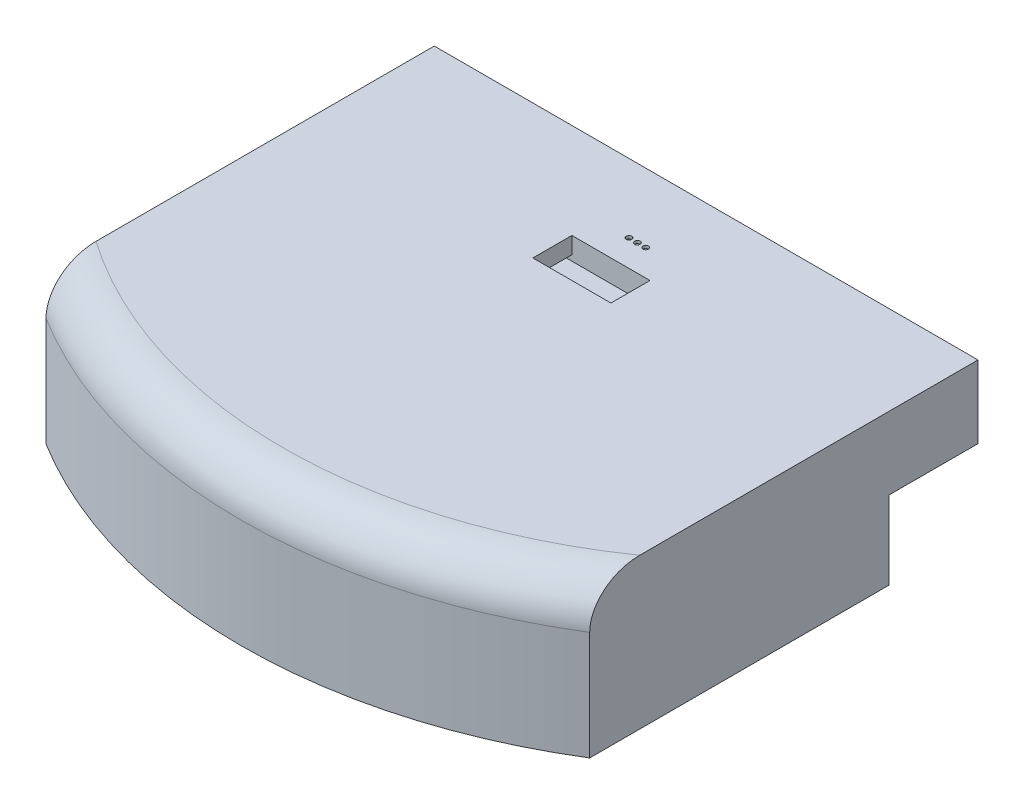
SolidWorks part; units mm, degrees
ref_plane "Front Plane" through (0, 0, 0) normal (0, 0, 1) x (1, 0, 0)
ref_plane "Top Plane" through (0, 0, 0) normal (0, 1, 0) x (1, 0, 0)
ref_plane "Right Plane" through (0, 0, 0) normal (1, 0, 0) x (0, 0, -1)
sketch "Sketch1" plane through (0, 0, 0) normal (0, 1, 0) x (1, 0, 0)
  line L0 (-97.5, -18.7714) -> (97.5, -18.7714)
  line L1 (97.5, -158.0314) -> (97.5, -18.7714)
  line L2 (-97.5, -18.7714) -> (-97.5, -158.0314)
  arc A0 (97.5, -158.0314) -> (-97.5, -158.0314) centre (0, 0) cw
  point P2 (0, 0)
  dimension "D2" = 195
  dimension "D3" = 139.26
extrude "Boss-Extrude1" add sketch "Sketch1" along normal blind 54
fillet "Fillet1" radius 15 1 edges at (0, 54, 185.6884)
sketch "Sketch2" plane through (-97.5, 0, 0) normal (-1, 0, 0) x (0, 0, 1)
  line L1 (18.7714, 0) -> (50.7714, 0)
  line L2 (18.7714, 0) -> (18.7714, 28)
  line L3 (18.7714, 28) -> (50.7714, 28)
  line L4 (50.7714, 0) -> (50.7714, 28)
  dimension "D1" = 28
  dimension "D2" = 32
extrude "Cut-Extrude1" cut sketch "Sketch2" against normal blind 445
sketch "Sketch3" plane through (0, 0, 0) normal (0, -1, 0) x (1, 0, 0)
  line L0 (0, 185.6884) -> (0, 159.7484)
  line L2 (-6.9, 159.7484) -> (6.9, 159.7484)
  line L3 (-6.9, 159.7484) -> (-6.9, 143.2484)
  line L4 (-6.9, 143.2484) -> (6.9, 143.2484)
  line L5 (6.9, 159.7484) -> (6.9, 143.2484)
  arc A0 (97.5, 158.0314) -> (-97.5, 158.0314) centre (0, 0) ccw construction
  dimension "D1" = 25.94
  dimension "D2" = 13.8
  dimension "D3" = 16.5
extrude "Boss-Extrude2" add sketch "Sketch3" along normal blind 5.5 contours L5 L2 L3 L4
sketch "Sketch4" plane through (0, 0, 143.2484) normal (0, 0, -1) x (-1, 0, 0)
  line L0 (6.9, -5.5) -> (6.9, 0) construction
  line L1 (-6.9, -5.5) -> (6.9, -5.5)
  line L2 (-6.9, -5.5) -> (-6.9, -2)
  line L3 (-6.9, -2) -> (6.9, -2)
  line L4 (6.9, -5.5) -> (6.9, -2)
  dimension "D1" = 3.5
extrude "Boss-Extrude3" add sketch "Sketch4" along normal blind 4
sketch "Sketch5" plane through (0, 54, 0) normal (0, 1, 0) x (1, 0, 0)
  circle A0 centre (0, -43.4388) radius 1
  circle A1 centre (3, -43.4388) radius 1
  circle A2 centre (-3, -43.4388) radius 1
  dimension "D1" = 2
  dimension "D2" = 2
  dimension "D3" = 2
extrude "Cut-Extrude2" cut sketch "Sketch5" against normal blind 1
sketch "Sketch6" plane through (0, 54, 0) normal (0, 1, 0) x (1, 0, 0)
  line L1 (-14, -66.9255) -> (14, -66.9255)
  line L2 (-14, -66.9255) -> (-14, -52.9255)
  line L3 (-14, -52.9255) -> (14, -52.9255)
  line L4 (14, -66.9255) -> (14, -52.9255)
  line L5 (-14, -66.9255) -> (14, -52.9255) construction
  line L6 (-14, -52.9255) -> (14, -66.9255) construction
  point P0 (0, -59.9255)
  point P5 (0, 0)
  dimension "D1" = 28
  dimension "D2" = 14
extrude "Cut-Extrude3" cut sketch "Sketch6" against normal blind 8
sketch "Sketch7" plane through (-14, 0, 0) normal (1, 0, 0) x (0, 0, -1)
  line L0 (-52.9255, 46) -> (-52.9255, 54) construction
  line L1 (-66.9255, 46) -> (-52.9255, 46)
  line L2 (-66.9255, 46) -> (-66.9255, 48)
  line L3 (-66.9255, 48) -> (-52.9255, 48)
  line L4 (-52.9255, 46) -> (-52.9255, 48)
  dimension "D1" = 2
extrude "Cut-Extrude4" cut sketch "Sketch7" against normal blind 3 and the other way blind 30
